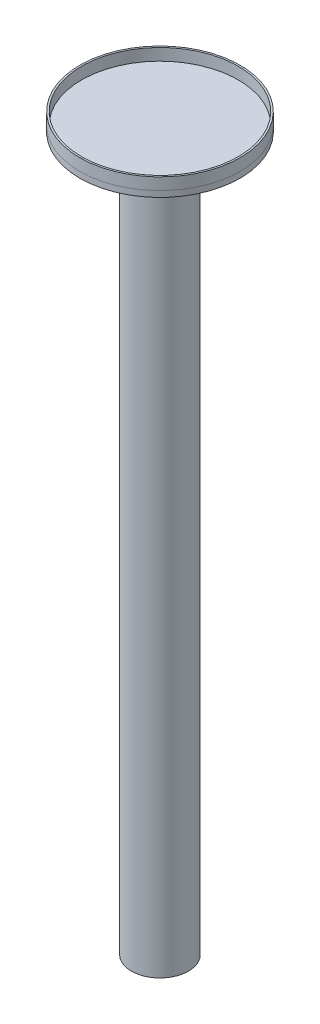
SolidWorks part; units mm, degrees
ref_plane "Front Plane" through (0, 0, 0) normal (0, 0, 1) x (1, 0, 0)
ref_plane "Top Plane" through (0, 0, 0) normal (0, 1, 0) x (1, 0, 0)
ref_plane "Right Plane" through (0, 0, 0) normal (1, 0, 0) x (0, 0, -1)
sketch "Sketch1" plane through (0, 0, 0) normal (0, 1, 0) x (1, 0, 0)
  circle A0 centre (0, 0) radius 24
  dimension "D1" = 48
extrude "Boss-Extrude1" add sketch "Sketch1" along normal blind 600
sketch "Sketch7" plane through (0, 600, 0) normal (0, 1, 0) x (1, 0, 0)
  circle A0 centre (0, 0) radius 67.5
  dimension "D1" = 135
extrude "Boss-Extrude5" add sketch "Sketch7" along normal blind 5
sketch "Sketch6" plane through (0, 605, 0) normal (0, 1, 0) x (1, 0, 0)
  circle A0 centre (0, 0) radius 66
  circle A1 centre (0, 0) radius 67.5
  dimension "D1" = 135
  dimension "D2" = 132
extrude "Boss-Extrude4" add sketch "Sketch6" along normal blind 10 separate body
